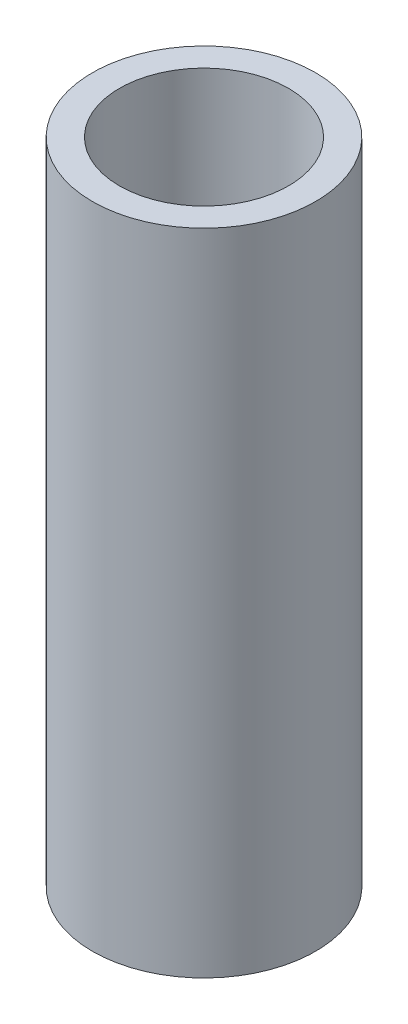
SolidWorks part; units mm, degrees
ref_plane "Front Plane" through (0, 0, 0) normal (0, 0, 1) x (1, 0, 0)
ref_plane "Top Plane" through (0, 0, 0) normal (0, 1, 0) x (1, 0, 0)
ref_plane "Right Plane" through (0, 0, 0) normal (1, 0, 0) x (0, 0, -1)
sketch "Sketch1" plane through (0, 0, 0) normal (0, 1, 0) x (1, 0, 0)
  circle A0 centre (0, 0) radius 13.0969
  circle A1 centre (0, 0) radius 9.9219
  dimension "D1" = 26.1937
  dimension "D2" = 19.8438
extrude "Boss-Extrude1" add sketch "Sketch1" along normal blind 76.2
